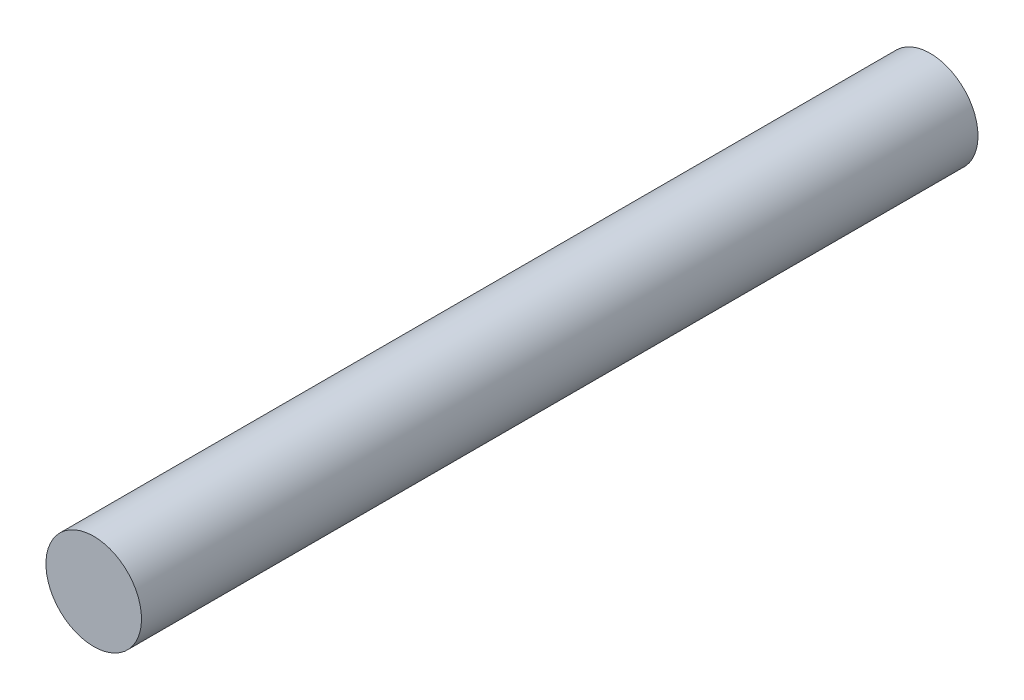
SolidWorks part; units mm, degrees
material "Plain Carbon Steel"
ref_plane "Front Plane" through (0, 0, 0) normal (0, 0, 1) x (1, 0, 0)
ref_plane "Top Plane" through (0, 0, 0) normal (0, 1, 0) x (1, 0, 0)
ref_plane "Right Plane" through (0, 0, 0) normal (1, 0, 0) x (0, 0, -1)
sketch "Sketch1" plane through (0, 0, 0) normal (0, 0, 1) x (1, 0, 0)
  circle A0 centre (0, 0) radius 4
  dimension "D1" = 8
extrude "Boss-Extrude1" add sketch "Sketch1" along normal blind 70
